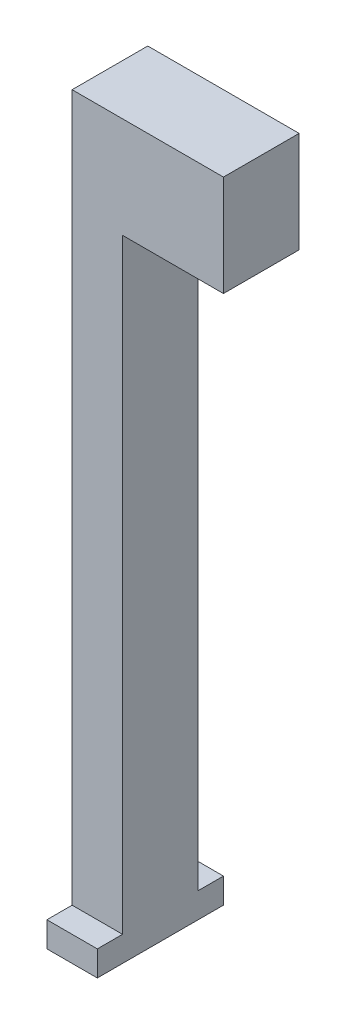
SolidWorks part; units mm, degrees
ref_plane "Front Plane" through (0, 0, 0) normal (0, 0, 1) x (1, 0, 0)
ref_plane "Top Plane" through (0, 0, 0) normal (0, 1, 0) x (1, 0, 0)
ref_plane "Right Plane" through (0, 0, 0) normal (1, 0, 0) x (0, 0, -1)
sketch "Sketch2" plane through (0, 0, 0) normal (0, 0, 1) x (1, 0, 0)
  line L1 (15, -10) -> (-15, -10)
  line L2 (15, -10) -> (15, 10)
  line L3 (15, 10) -> (-15, 10)
  line L4 (-15, -10) -> (-15, 10)
  line L5 (15, -10) -> (-15, 10) construction
  line L6 (15, 10) -> (-15, -10) construction
  line L7 (-15, -10) -> (-5, -10)
  line L8 (-15, -10) -> (-15, -130)
  line L9 (-15, -130) -> (-5, -130)
  line L10 (-5, -10) -> (-5, -130)
  point P0 (0, 0)
  dimension "D1" = 30
  dimension "D2" = 20
  dimension "D3" = 10
  dimension "D4" = 120
extrude "Boss-Extrude1" add sketch "Sketch2" along normal blind 15 contours L4 L1 L2 L3 | L10 L1 L8 L9
sketch "Sketch3" plane through (0, 0, 15) normal (0, 0, 1) x (1, 0, 0)
  line L1 (-15, -130) -> (-5, -130)
  line L2 (-15, -130) -> (-15, -135)
  line L3 (-15, -135) -> (-5, -135)
  line L4 (-5, -130) -> (-5, -135)
  dimension "D1" = 5
extrude "Boss-Extrude2" add sketch "Sketch3" along normal blind 5 and the other way blind 20
sketch "Sketch5" plane through (0, -10, 0) normal (0, -1, 0) x (1, 0, 0)
  line L0 (15, 15) -> (-5, 15) construction
  line L1 (15, 15) -> (15, 0) construction
  circle A0 centre (5, 7.5) radius 2.5173
  dimension "D1" = 7.5
  dimension "D2" = 10
extrude "Cut-Extrude1" cut sketch "Sketch5" against normal blind 1
